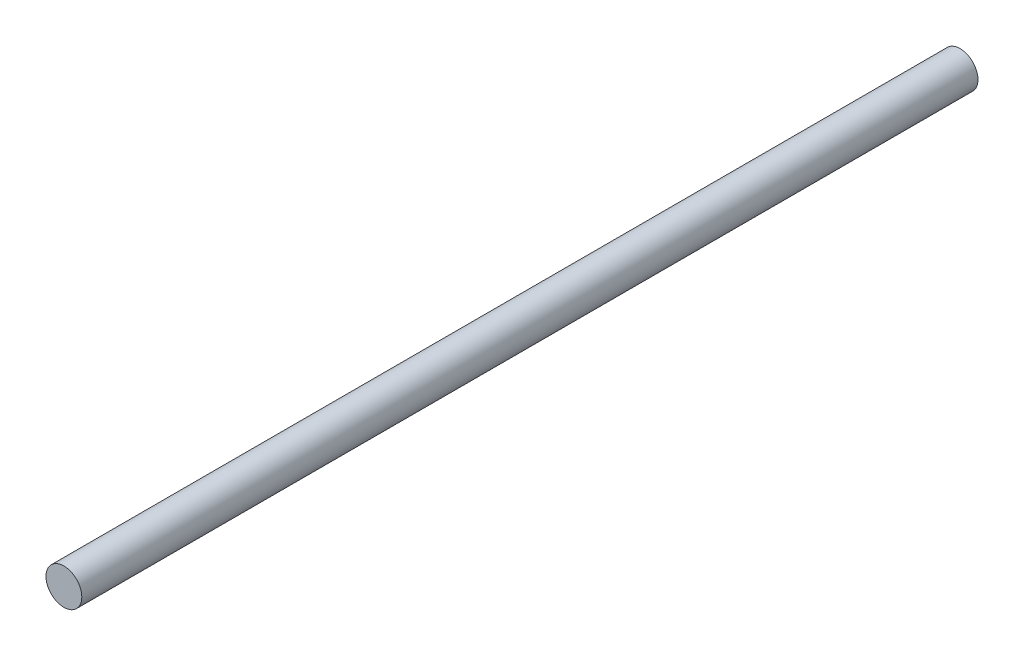
SolidWorks part; units mm, degrees
ref_plane "Alzado" through (0, 0, 0) normal (0, 0, 1) x (1, 0, 0)
ref_plane "Planta" through (0, 0, 0) normal (0, 1, 0) x (1, 0, 0)
ref_plane "Vista lateral" through (0, 0, 0) normal (1, 0, 0) x (0, 0, -1)
sketch "Croquis1" plane through (0, 0, 0) normal (0, 0, 1) x (1, 0, 0)
  circle A0 centre (0, 0) radius 2
extrude "Saliente-Extruir1" add sketch "Croquis1" along normal blind 100
